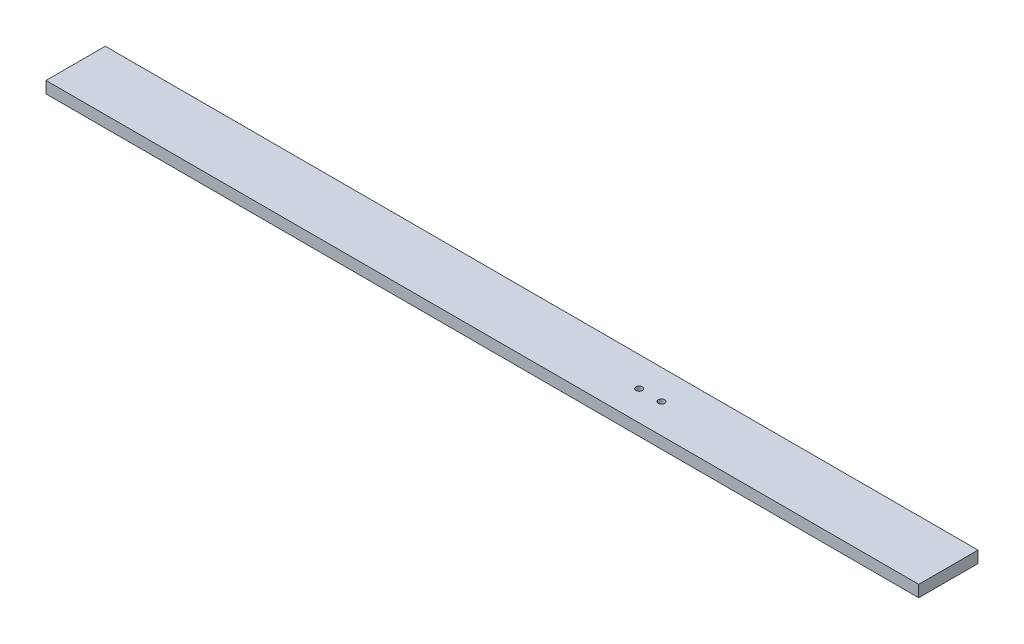
SolidWorks part; units mm, degrees
ref_plane "Alzado" through (0, 0, 0) normal (0, 0, 1) x (1, 0, 0)
ref_plane "Planta" through (0, 0, 0) normal (0, 1, 0) x (1, 0, 0)
ref_plane "Vista lateral" through (0, 0, 0) normal (1, 0, 0) x (0, 0, -1)
sketch "Croquis1" plane through (0, 0, 0) normal (0, 1, 0) x (1, 0, 0)
  line L1 (-374, 25.4) -> (374, 25.4)
  line L2 (-374, 25.4) -> (-374, -25.4)
  line L3 (-374, -25.4) -> (374, -25.4)
  line L4 (374, 25.4) -> (374, -25.4)
  line L5 (-374, 25.4) -> (374, -25.4) construction
  line L6 (-374, -25.4) -> (374, 25.4) construction
  point P0 (0, 0)
  dimension "D1" = 50.8
  dimension "D2" = 748
extrude "Saliente-Extruir1" add sketch "Croquis1" along normal blind 10
sketch "Croquis2" plane through (0, 10, 0) normal (0, 1, 0) x (1, 0, 0)
  line L0 (128.1, 25.4) -> (128.1, -25.4) construction
  line L1 (374, 25.4) -> (-374, 25.4) construction
  line L2 (-374, -25.4) -> (374, -25.4) construction
  line L4 (374, -25.4) -> (374, 25.4) construction
  line L5 (-374, 0) -> (374, 0) construction
  line L6 (-374, 25.4) -> (-374, -25.4) construction
  circle A0 centre (128.1, 0) radius 2.75
  circle A1 centre (109, 0) radius 2.75
  dimension "D2" = 19.1
  dimension "D3" = 5.5
  dimension "D1" = 245.9
extrude "Cortar-Extruir1" cut sketch "Croquis2" against normal through all
